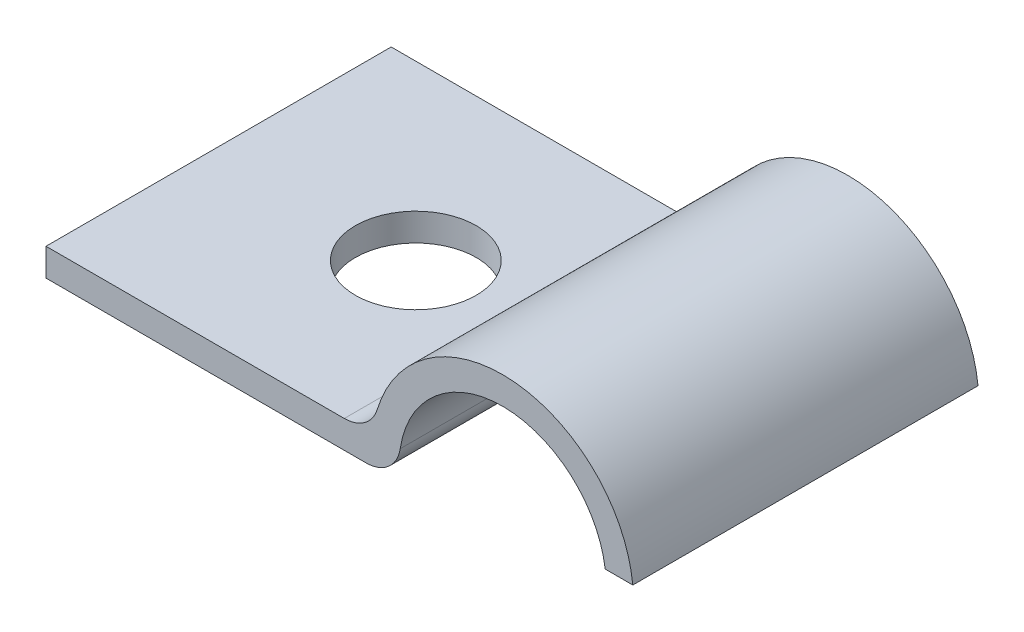
SolidWorks part; units mm, degrees
ref_plane "Front" through (0, 0, 0) normal (0, 0, 1) x (1, 0, 0)
ref_plane "Top" through (0, 0, 0) normal (0, 1, 0) x (1, 0, 0)
ref_plane "Right" through (0, 0, 0) normal (1, 0, 0) x (0, 0, -1)
sketch "Sketch2" plane through (0, 0, 0) normal (0, 0, 1) x (1, 0, 0)
  line L0 (0, 0) -> (10.2536, 0)
  line L1 (0, 0) -> (0, 0.8)
  line L2 (0, 0.8) -> (9.4536, 0.8)
  line L3 (16.2, 0.8) -> (17, 0.8)
  line L4 (0, 0.4) -> (13.2268, 0.4) construction
  circle A0 centre (13.2268, 0.4) radius 3 construction
  arc A1 (9.4536, 0.8) -> (17, 0.8) centre (13.2268, 0.4) cw
  arc A2 (10.2536, 0) -> (16.2, 0.8) centre (13.2268, 0.4) cw
  dimension "D1" = 6
  dimension "D2" = 0.8
  dimension "D3" = 17
extrude "Boss-Extrude1" add sketch "Sketch2" along normal blind 10
fillet "Fillet1" radius 1 2 edges at (9.4536, 0.8, 5) (10.2536, 0, 5)
sketch "Sketch3" plane through (0, 0.8, 0) normal (0, 1, 0) x (1, 0, 0)
  line L0 (0, -5) -> (5.7134, -5) construction
  line L1 (0, -10) -> (0, 0) construction
  line L2 (13.2134, 0) -> (13.2134, -5) construction
  line L3 (10.2268, 0) -> (16.2, 0) construction
  line L4 (13.2134, -5) -> (5.7134, -5) construction
  circle A0 centre (5.7134, -5) radius 1.75
  dimension "D1" = 3.5
  dimension "D2" = 7.5
extrude "Cut-Extrude1" cut sketch "Sketch3" against normal through all
